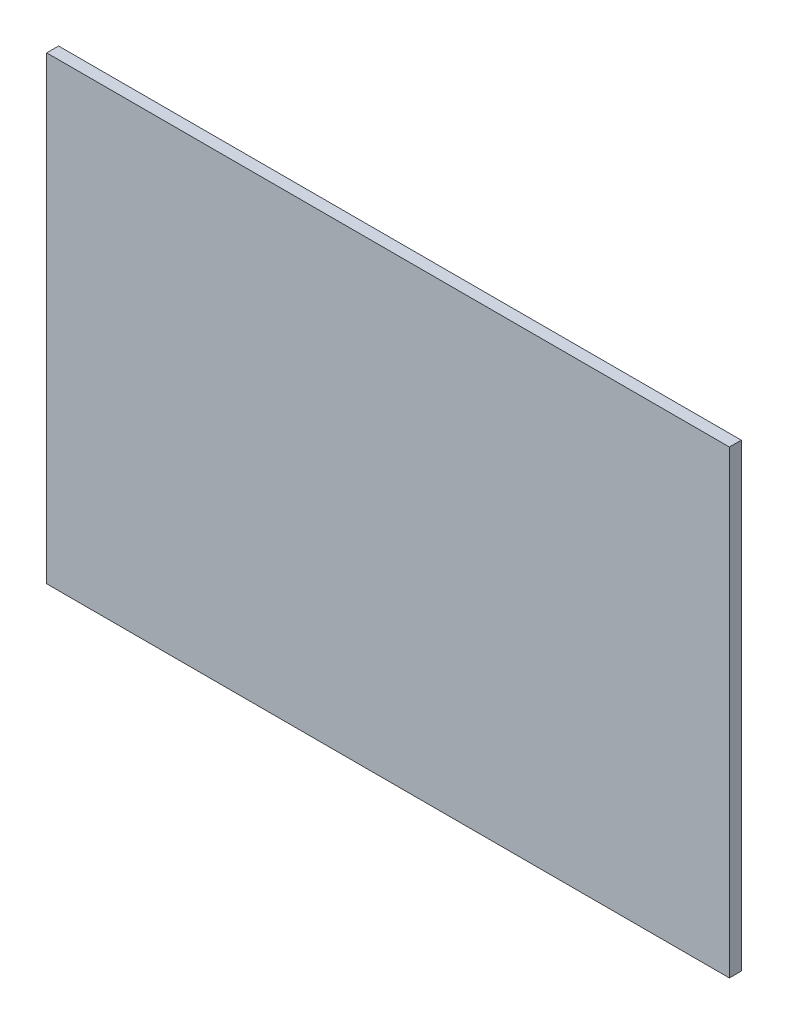
SolidWorks part; units mm, degrees
ref_plane "Front Plane" through (0, 0, 0) normal (0, 0, 1) x (1, 0, 0)
ref_plane "Top Plane" through (0, 0, 0) normal (0, 1, 0) x (1, 0, 0)
ref_plane "Right Plane" through (0, 0, 0) normal (1, 0, 0) x (0, 0, -1)
sketch "Sketch1" plane through (0, 0, 0) normal (0, 0, 1) x (1, 0, 0)
  line L1 (-66.4703, 30.5762) -> (79.3772, 30.5762)
  line L2 (-66.4703, 30.5762) -> (-66.4703, -67.6617)
  line L3 (-66.4703, -67.6617) -> (79.3772, -67.6617)
  line L4 (79.3772, 30.5762) -> (79.3772, -67.6617)
extrude "Boss-Extrude1" add sketch "Sketch1" along normal blind 2.54
sketch "Sketch2" plane through (0, 0, 2.54) normal (0, 0, 1) x (1, 0, 0)
  circle A0 centre (6.5263, -14.1572) radius 11.3865
  circle A1 centre (6.5263, -14.1572) radius 10.7104
  spline S0 degree 3 poles (-2.078, -20.5352) (5.098, -18.9253) (10.697, -12.443) (13.0715, -5.6793) knots 0 0 0 0 1 1 1 1
  spline S1 degree 3 poles (-1.68, -21.0397) (2.041, -19.6124) (10.1846, -20.0497) (17.1237, -13.0906) (15.7025, -8.6335) knots 0 0 0 0 0.490314 1 1 1 1
